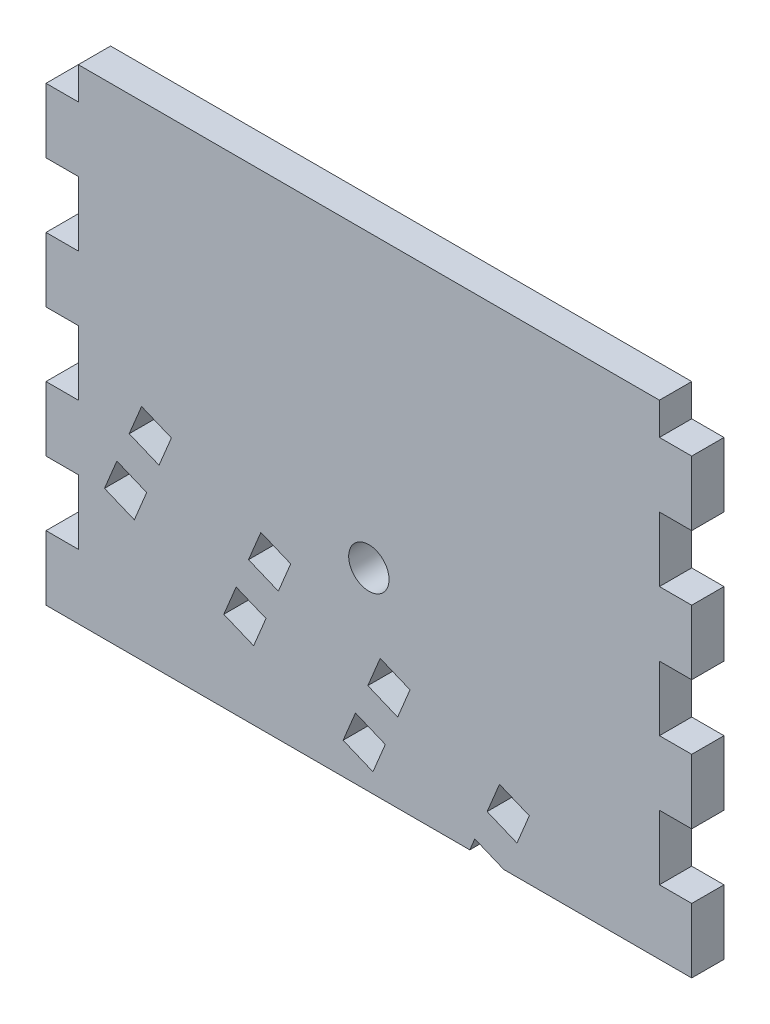
SolidWorks part; units mm, degrees
material "Pine"
ref_plane "Front Plane" through (0, 0, 0) normal (0, 0, 1) x (1, 0, 0)
ref_plane "Top Plane" through (0, 0, 0) normal (0, 1, 0) x (1, 0, 0)
ref_plane "Right Plane" through (0, 0, 0) normal (1, 0, 0) x (0, 0, -1)
sketch "Sketch1" plane through (0, 0, 0) normal (0, 0, 1) x (1, 0, 0)
  line L1 (0, 0) -> (127, 0)
  line L2 (0, 0) -> (0, 95.25)
  line L3 (0, 95.25) -> (127, 95.25)
  line L4 (127, 0) -> (127, 95.25)
  dimension "D1" = 127
  dimension "D2" = 95.25
extrude "Boss-Extrude1" add sketch "Sketch1" along normal blind 6.35
sketch "Sketch2" plane through (0, 0, 6.35) normal (0, 0, 1) x (1, 0, 0)
  line L0 (0, 95.25) -> (0, 0) construction
  line L1 (0, 0) -> (127, 0) construction
  circle A0 centre (63.5, 38.1) radius 3.9687
  dimension "D3" = 7.9375
  dimension "D1" = 63.5
  dimension "D2" = 38.1
extrude "Cut-Extrude1" cut sketch "Sketch2" against normal through all
sketch "Sketch3" plane through (0, 0, 6.35) normal (0, 0, 1) x (1, 0, 0)
  line L0 (0, 95.25) -> (0, 0) construction
  line L1 (0, 12.7) -> (6.35, 12.7)
  line L2 (0, 12.7) -> (0, 25.4)
  line L3 (0, 25.4) -> (6.35, 25.4)
  line L4 (6.35, 12.7) -> (6.35, 25.4)
  dimension "D1" = 6.35
  dimension "D2" = 12.7
  dimension "D3" = 12.7
extrude "Cut-Extrude2" cut sketch "Sketch3" against normal through all
sketch "Sketch4" plane through (0, 0, 6.35) normal (0, 0, 1) x (1, 0, 0)
  line L0 (127, 0) -> (127, 95.25) construction
  line L1 (127, 12.7) -> (120.65, 12.7)
  line L2 (127, 12.7) -> (127, 25.4)
  line L3 (127, 25.4) -> (120.65, 25.4)
  line L4 (120.65, 12.7) -> (120.65, 25.4)
  line L5 (6.35, 12.7) -> (6.35, 25.4) construction
  line L6 (0, 12.7) -> (6.35, 12.7) construction
extrude "Cut-Extrude3" cut sketch "Sketch4" against normal through all
pattern_linear "LPattern1" count 4 spacing 25.4 along (0, 1, 0) of "Cut-Extrude2", "Cut-Extrude3"
sketch "Sketch5" plane through (0, 0, 6.35) normal (0, 0, 1) x (1, 0, 0)
  line L0 (6.35, 38.1) -> (98.3315, 0) construction
  line L1 (0, 0) -> (127, 0) construction
  line L2 (15.6532, 27.3733) -> (20.5133, 39.1066) construction
  line L3 (24.6616, 40.8249) -> (22.2316, 34.9582)
  line L4 (24.6616, 40.8249) -> (18.795, 43.2549)
  line L5 (22.2316, 34.9582) -> (16.365, 37.3883)
  line L6 (18.795, 43.2549) -> (16.365, 37.3883)
  line L7 (24.6616, 40.8249) -> (16.365, 37.3883) construction
  line L8 (22.2316, 34.9582) -> (18.795, 43.2549) construction
  line L9 (17.3715, 23.2249) -> (19.8016, 29.0916)
  line L10 (17.3715, 23.2249) -> (11.5049, 25.655)
  line L11 (19.8016, 29.0916) -> (13.9349, 31.5216)
  line L12 (11.5049, 25.655) -> (13.9349, 31.5216)
  line L13 (17.3715, 23.2249) -> (13.9349, 31.5216) construction
  line L14 (19.8016, 29.0916) -> (11.5049, 25.655) construction
  point P7 (18.0833, 33.2399)
  dimension "D1" = 22.5
  dimension "D2" = 6.35
  dimension "D3" = 6.35
  dimension "D4" = 12.7
  dimension "D5" = 6.35
extrude "Cut-Extrude4" cut sketch "Sketch5" against normal through all
pattern_linear "LPattern2" count 4 spacing 25.4 along (0.9239, -0.3827, 0) of "Cut-Extrude4"
